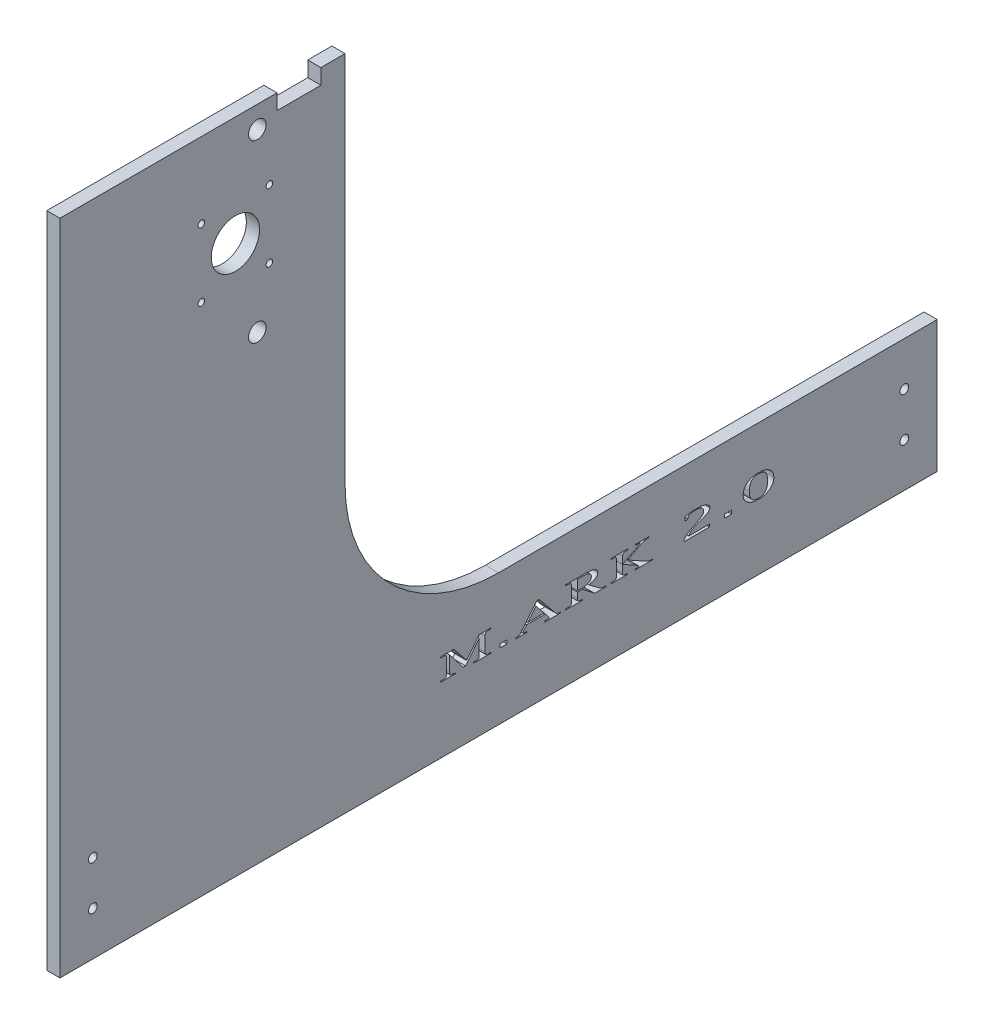
SolidWorks part; units mm, degrees
material "Acrylic (Medium-high impact)"
ref_plane "Front Plane" through (0, 0, 0) normal (0, 0, 1) x (1, 0, 0)
ref_plane "Top Plane" through (0, 0, 0) normal (0, 1, 0) x (1, 0, 0)
ref_plane "Right Plane" through (0, 0, 0) normal (1, 0, 0) x (0, 0, -1)
sketch "Sketch1" plane through (0, 0, 0) normal (1, 0, 0) x (0, 0, -1)
  line L0 (-1000, 0) -> (49000, 0) construction
  line L1 (-80, -300) -> (320, -300)
  line L4 (320, -300) -> (320, -240)
  line L6 (-80, -300) -> (-80, -240)
  line L7 (0, -1000) -> (0, 49000) construction
  line L10 (-30, 0) -> (-30, -170)
  line L11 (-1080, -240) -> (48920, -240) construction
  line L12 (-112.889, -170) -> (172.771, -170) construction
  line L20 (0, -750) -> (0, 49250) construction
  line L31 (50, 0) -> (50, -170)
  line L33 (120, -240) -> (320, -240)
  line L34 (-7.1942, -50) -> (7.1942, -50) construction
  line L37 (-30, 0) -> (50, 0)
  line L38 (10, -1000) -> (10, 49000) construction
  circle A2 centre (10, -90) radius 4
  circle A3 centre (10, -10) radius 4
  circle A4 centre (15.5, -34.5) radius 1.5
  arc A5 (120, -240) -> (50, -170) centre (120, -170) cw
  circle A6 centre (-15.5, -34.5) radius 1.5
  circle A7 centre (15.5, -65.5) radius 1.5
  circle A8 centre (-15.5, -65.5) radius 1.5
  circle A9 centre (0, -50) radius 11
  arc A12 (-80, -240) -> (-30, -170) centre (-104, -170) ccw
  point P0 (0, 0)
  point P51 (0, -50)
  point P62 (0, 0)
  dimension "D7" = 8
  dimension "D14" = 60
  dimension "D16" = 50
  dimension "D18" = 3
  dimension "D10" = 70
  dimension "D23" = 120
  dimension "D6" = 22
  dimension "D3" = 400
  dimension "D4" = 30
  dimension "D5" = 170
  dimension "D8" = 300
  dimension "D9" = 60
  dimension "D11" = 50
  dimension "D12" = 130
  dimension "D13" = 70
  dimension "D15" = 10
  dimension "D17" = 40
  dimension "D19" = 15.5
  dimension "D21" = 50
  dimension "D22" = 10
extrude "Boss-Extrude1" add sketch "Sketch1" along normal blind 6 contours L37 L31 A5 L33 L4 L1
sketch "Sketch2" plane through (0, 0, 0) normal (-1, 0, 0) x (0, 0, 1)
  line L0 (30, 0) -> (30, -170) construction
  line L1 (80, -300) -> (30, -300)
  line L2 (80, -300) -> (80, 0)
  line L3 (80, 0) -> (30, 0)
  line L4 (30, -300) -> (30, 0)
  line L5 (-50, 0) -> (30, 0) construction
extrude "Boss-Extrude2" add sketch "Sketch2" against normal blind 6
sketch "Sketch3" plane through (6, 0, 0) normal (1, 0, 0) x (0, 0, -1)
  line L0 (50, 0) -> (-80, 0) construction
  line L1 (39, -7) -> (19, -7)
  line L2 (39, -7) -> (39, 0)
  line L3 (39, 0) -> (19, 0)
  line L4 (19, -7) -> (19, 0)
  circle A0 centre (10, -10) radius 4 construction
  dimension "D1" = 7
  dimension "D2" = 20
  dimension "D3" = 9
extrude "Cut-Extrude1" cut sketch "Sketch3" against normal up to next
sketch "Sketch4" plane through (6, 0, 0) normal (1, 0, 0) x (0, 0, -1)
  line L0 (-80, -300) -> (320, -300) construction
  line L1 (-80, 0) -> (-80, -300) construction
  line L2 (-708, -270) -> (49292, -270) construction
  line L3 (120, -1300) -> (120, 48700) construction
  circle A0 centre (-65, -280) radius 2
  circle A1 centre (-65, -260) radius 2
  circle A2 centre (305, -260) radius 2
  circle A3 centre (305, -280) radius 2
  point P11 (120, -300)
  dimension "D1" = 4
  dimension "D2" = 20
  dimension "D3" = 15
  dimension "D4" = 30
extrude "Cut-Extrude2" cut sketch "Sketch4" against normal up to next
sketch "Sketch7" plane through (0, 0, 0) normal (-1, 0, 0) x (0, 0, 1)
  line L0 (-170, -1300) -> (-170, 48700) construction
  line L1 (80, -300) -> (-320, -300) construction
  line L2 (-270.017, -270) -> (-69.983, -270) construction
  line L3 (-320, -300) -> (-320, -240) construction
  text T0 "M.ARK 2.0" font "Lucida Bright" height 10
  point P8 (-170, -270)
  point P10 (-122.5795, -270)
  point P12 (-245.6238, -270)
  point P13 (-69.983, -270)
  dimension "D1" = 30
  dimension "D2" = 150
extrude "Cut-Extrude4" cut sketch "Sketch7" against normal through all
